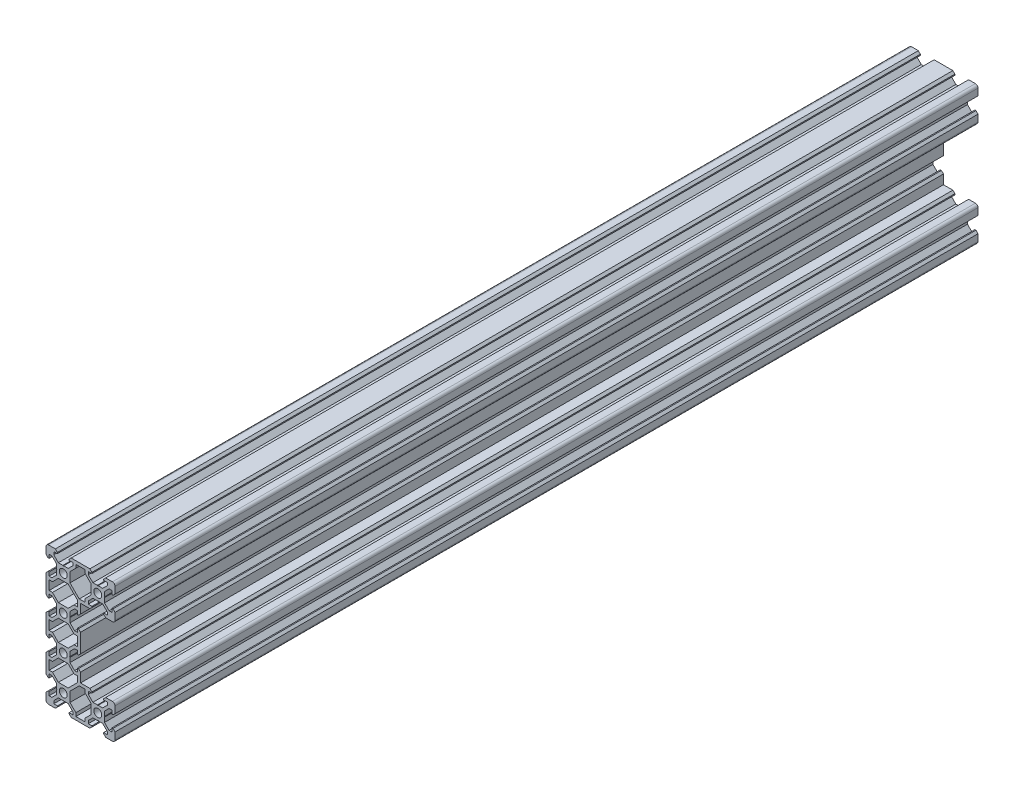
SolidWorks part; units mm, degrees
material "6061-T6 (SS)"
ref_plane "Front Plane" through (0, 0, 0) normal (0, 0, 1) x (1, 0, 0)
ref_plane "Top Plane" through (0, 0, 0) normal (0, 1, 0) x (1, 0, 0)
ref_plane "Right Plane" through (0, 0, 0) normal (1, 0, 0) x (0, 0, -1)
sketch "Sketch1" plane through (0, 0, 0) normal (0, 0, 1) x (1, 0, 0)
  line L0 (-20, -38.5) -> (-20, 38.5)
  line L1 (-18.5, 40) -> (18.5, 40)
  line L2 (20, 38.5) -> (20, 21.5)
  line L3 (18.5, 20) -> (0, 20)
  line L4 (0, 20) -> (0, -20)
  line L5 (0, 0) -> (-20, 0) construction
  line L6 (18.5, -20) -> (0, -20)
  line L7 (20, -38.5) -> (20, -21.5)
  line L8 (-18.5, -40) -> (18.5, -40)
  line L9 (20, 30) -> (10, 30) construction
  line L10 (-10, 0) -> (-10, 10) construction
  arc A0 (-18.5, -40) -> (-20, -38.5) centre (-18.5, -38.5) cw
  arc A1 (20, -38.5) -> (18.5, -40) centre (18.5, -38.5) cw
  arc A2 (18.5, -20) -> (20, -21.5) centre (18.5, -21.5) cw
  arc A3 (20, 21.5) -> (18.5, 20) centre (18.5, 21.5) cw
  arc A4 (18.5, 40) -> (20, 38.5) centre (18.5, 38.5) cw
  arc A5 (-20, 38.5) -> (-18.5, 40) centre (-18.5, 38.5) cw
  circle A6 centre (10, 30) radius 2.3
  circle A7 centre (-10, 30) radius 2.3
  circle A8 centre (-10, 10) radius 2.3
  circle A9 centre (-10, -10) radius 2.3
  circle A10 centre (10, -30) radius 2.3
  circle A11 centre (-10, -30) radius 2.3
  point P13 (-20, -40)
  point P16 (20, -40)
  point P19 (20, -20)
  point P22 (20, 20)
  point P25 (20, 40)
  point P28 (-20, 40)
  line B0 (-10, 30) -> (-10, 40) construction
  line B1 (-10, 33.69) -> (-10.21, 33.9)
  line B2 (-10.21, 33.9) -> (-12.8393, 33.9)
  line B3 (-12.8393, 33.9) -> (-15.5, 36.5607)
  line B4 (-15.5, 36.5607) -> (-15.5, 38.2)
  line B5 (-15.5, 38.2) -> (-13.395, 38.2)
  line B6 (-13.395, 38.2) -> (-13.395, 38.815)
  line B7 (-13.395, 38.815) -> (-14.58, 40)
  line B8 (-14.58, 40) -> (-5.42, 40)
  line B9 (-10, 30) -> (-15.9132, 35.9132) construction
  line B10 (-6.605, 38.815) -> (-5.42, 40)
  line B11 (-6.605, 38.2) -> (-6.605, 38.815)
  line B12 (-4.5, 38.2) -> (-6.605, 38.2)
  line B13 (-4.5, 36.5607) -> (-4.5, 38.2)
  line B14 (-7.1607, 33.9) -> (-4.5, 36.5607)
  line B15 (-9.79, 33.9) -> (-7.1607, 33.9)
  line B16 (-10, 33.69) -> (-9.79, 33.9)
  line B17 (10, 30) -> (10, 40) construction
  line B18 (10, 33.69) -> (9.79, 33.9)
  line B19 (9.79, 33.9) -> (7.1607, 33.9)
  line B20 (7.1607, 33.9) -> (4.5, 36.5607)
  line B21 (4.5, 36.5607) -> (4.5, 38.2)
  line B22 (4.5, 38.2) -> (6.605, 38.2)
  line B23 (6.605, 38.2) -> (6.605, 38.815)
  line B24 (6.605, 38.815) -> (5.42, 40)
  line B25 (5.42, 40) -> (14.58, 40)
  line B26 (10, 30) -> (4.0868, 35.9132) construction
  line B27 (13.395, 38.815) -> (14.58, 40)
  line B28 (13.395, 38.2) -> (13.395, 38.815)
  line B29 (15.5, 38.2) -> (13.395, 38.2)
  line B30 (15.5, 36.5607) -> (15.5, 38.2)
  line B31 (12.8393, 33.9) -> (15.5, 36.5607)
  line B32 (10.21, 33.9) -> (12.8393, 33.9)
  line B33 (10, 33.69) -> (10.21, 33.9)
  line B34 (10, -30) -> (10, -20) construction
  line B35 (10, -26.31) -> (9.79, -26.1)
  line B36 (9.79, -26.1) -> (7.1607, -26.1)
  line B37 (7.1607, -26.1) -> (4.5, -23.4393)
  line B38 (4.5, -23.4393) -> (4.5, -21.8)
  line B39 (4.5, -21.8) -> (6.605, -21.8)
  line B40 (6.605, -21.8) -> (6.605, -21.185)
  line B41 (6.605, -21.185) -> (5.42, -20)
  line B42 (5.42, -20) -> (14.58, -20)
  line B43 (10, -30) -> (4.0868, -24.0868) construction
  line B44 (13.395, -21.185) -> (14.58, -20)
  line B45 (13.395, -21.8) -> (13.395, -21.185)
  line B46 (15.5, -21.8) -> (13.395, -21.8)
  line B47 (15.5, -23.4393) -> (15.5, -21.8)
  line B48 (12.8393, -26.1) -> (15.5, -23.4393)
  line B49 (10.21, -26.1) -> (12.8393, -26.1)
  line B50 (10, -26.31) -> (10.21, -26.1)
  line B51 (-10, 30) -> (-20, 30) construction
  line B52 (-13.69, 30) -> (-13.9, 29.79)
  line B53 (-13.9, 29.79) -> (-13.9, 27.1607)
  line B54 (-13.9, 27.1607) -> (-16.5607, 24.5)
  line B55 (-16.5607, 24.5) -> (-18.2, 24.5)
  line B56 (-18.2, 24.5) -> (-18.2, 26.605)
  line B57 (-18.2, 26.605) -> (-18.815, 26.605)
  line B58 (-18.815, 26.605) -> (-20, 25.42)
  line B59 (-20, 25.42) -> (-20, 34.58)
  line B60 (-10, 30) -> (-15.9132, 24.0868) construction
  line B61 (-18.815, 33.395) -> (-20, 34.58)
  line B62 (-18.2, 33.395) -> (-18.815, 33.395)
  line B63 (-18.2, 35.5) -> (-18.2, 33.395)
  line B64 (-16.5607, 35.5) -> (-18.2, 35.5)
  line B65 (-13.9, 32.8393) -> (-16.5607, 35.5)
  line B66 (-13.9, 30.21) -> (-13.9, 32.8393)
  line B67 (-13.69, 30) -> (-13.9, 30.21)
  line B68 (-10, 10) -> (-20, 10) construction
  line B69 (-13.69, 10) -> (-13.9, 9.79)
  line B70 (-13.9, 9.79) -> (-13.9, 7.1607)
  line B71 (-13.9, 7.1607) -> (-16.5607, 4.5)
  line B72 (-16.5607, 4.5) -> (-18.2, 4.5)
  line B73 (-18.2, 4.5) -> (-18.2, 6.605)
  line B74 (-18.2, 6.605) -> (-18.815, 6.605)
  line B75 (-18.815, 6.605) -> (-20, 5.42)
  line B76 (-20, 5.42) -> (-20, 14.58)
  line B77 (-10, 10) -> (-15.9132, 4.0868) construction
  line B78 (-18.815, 13.395) -> (-20, 14.58)
  line B79 (-18.2, 13.395) -> (-18.815, 13.395)
  line B80 (-18.2, 15.5) -> (-18.2, 13.395)
  line B81 (-16.5607, 15.5) -> (-18.2, 15.5)
  line B82 (-13.9, 12.8393) -> (-16.5607, 15.5)
  line B83 (-13.9, 10.21) -> (-13.9, 12.8393)
  line B84 (-13.69, 10) -> (-13.9, 10.21)
  line B85 (-10, -10) -> (-20, -10) construction
  line B86 (-13.69, -10) -> (-13.9, -10.21)
  line B87 (-13.9, -10.21) -> (-13.9, -12.8393)
  line B88 (-13.9, -12.8393) -> (-16.5607, -15.5)
  line B89 (-16.5607, -15.5) -> (-18.2, -15.5)
  line B90 (-18.2, -15.5) -> (-18.2, -13.395)
  line B91 (-18.2, -13.395) -> (-18.815, -13.395)
  line B92 (-18.815, -13.395) -> (-20, -14.58)
  line B93 (-20, -14.58) -> (-20, -5.42)
  line B94 (-10, -10) -> (-15.9132, -15.9132) construction
  line B95 (-18.815, -6.605) -> (-20, -5.42)
  line B96 (-18.2, -6.605) -> (-18.815, -6.605)
  line B97 (-18.2, -4.5) -> (-18.2, -6.605)
  line B98 (-16.5607, -4.5) -> (-18.2, -4.5)
  line B99 (-13.9, -7.1607) -> (-16.5607, -4.5)
  line B100 (-13.9, -9.79) -> (-13.9, -7.1607)
  line B101 (-13.69, -10) -> (-13.9, -9.79)
  line B102 (-10, -30) -> (-20, -30) construction
  line B103 (-13.69, -30) -> (-13.9, -30.21)
  line B104 (-13.9, -30.21) -> (-13.9, -32.8393)
  line B105 (-13.9, -32.8393) -> (-16.5607, -35.5)
  line B106 (-16.5607, -35.5) -> (-18.2, -35.5)
  line B107 (-18.2, -35.5) -> (-18.2, -33.395)
  line B108 (-18.2, -33.395) -> (-18.815, -33.395)
  line B109 (-18.815, -33.395) -> (-20, -34.58)
  line B110 (-20, -34.58) -> (-20, -25.42)
  line B111 (-10, -30) -> (-15.9132, -35.9132) construction
  line B112 (-18.815, -26.605) -> (-20, -25.42)
  line B113 (-18.2, -26.605) -> (-18.815, -26.605)
  line B114 (-18.2, -24.5) -> (-18.2, -26.605)
  line B115 (-16.5607, -24.5) -> (-18.2, -24.5)
  line B116 (-13.9, -27.1607) -> (-16.5607, -24.5)
  line B117 (-13.9, -29.79) -> (-13.9, -27.1607)
  line B118 (-13.69, -30) -> (-13.9, -29.79)
  line B119 (-10, -30) -> (-10, -40) construction
  line B120 (-10, -33.69) -> (-9.79, -33.9)
  line B121 (-9.79, -33.9) -> (-7.1607, -33.9)
  line B122 (-7.1607, -33.9) -> (-4.5, -36.5607)
  line B123 (-4.5, -36.5607) -> (-4.5, -38.2)
  line B124 (-4.5, -38.2) -> (-6.605, -38.2)
  line B125 (-6.605, -38.2) -> (-6.605, -38.815)
  line B126 (-6.605, -38.815) -> (-5.42, -40)
  line B127 (-5.42, -40) -> (-14.58, -40)
  line B128 (-10, -30) -> (-4.0868, -35.9132) construction
  line B129 (-13.395, -38.815) -> (-14.58, -40)
  line B130 (-13.395, -38.2) -> (-13.395, -38.815)
  line B131 (-15.5, -38.2) -> (-13.395, -38.2)
  line B132 (-15.5, -36.5607) -> (-15.5, -38.2)
  line B133 (-12.8393, -33.9) -> (-15.5, -36.5607)
  line B134 (-10.21, -33.9) -> (-12.8393, -33.9)
  line B135 (-10, -33.69) -> (-10.21, -33.9)
  line B136 (10, -30) -> (10, -40) construction
  line B137 (10, -33.69) -> (10.21, -33.9)
  line B138 (10.21, -33.9) -> (12.8393, -33.9)
  line B139 (12.8393, -33.9) -> (15.5, -36.5607)
  line B140 (15.5, -36.5607) -> (15.5, -38.2)
  line B141 (15.5, -38.2) -> (13.395, -38.2)
  line B142 (13.395, -38.2) -> (13.395, -38.815)
  line B143 (13.395, -38.815) -> (14.58, -40)
  line B144 (14.58, -40) -> (5.42, -40)
  line B145 (10, -30) -> (15.9132, -35.9132) construction
  line B146 (6.605, -38.815) -> (5.42, -40)
  line B147 (6.605, -38.2) -> (6.605, -38.815)
  line B148 (4.5, -38.2) -> (6.605, -38.2)
  line B149 (4.5, -36.5607) -> (4.5, -38.2)
  line B150 (7.1607, -33.9) -> (4.5, -36.5607)
  line B151 (9.79, -33.9) -> (7.1607, -33.9)
  line B152 (10, -33.69) -> (9.79, -33.9)
  line B153 (10, 30) -> (10, 20) construction
  line B154 (10, 26.31) -> (10.21, 26.1)
  line B155 (10.21, 26.1) -> (12.8393, 26.1)
  line B156 (12.8393, 26.1) -> (15.5, 23.4393)
  line B157 (15.5, 23.4393) -> (15.5, 21.8)
  line B158 (15.5, 21.8) -> (13.395, 21.8)
  line B159 (13.395, 21.8) -> (13.395, 21.185)
  line B160 (13.395, 21.185) -> (14.58, 20)
  line B161 (14.58, 20) -> (5.42, 20)
  line B162 (10, 30) -> (15.9132, 24.0868) construction
  line B163 (6.605, 21.185) -> (5.42, 20)
  line B164 (6.605, 21.8) -> (6.605, 21.185)
  line B165 (4.5, 21.8) -> (6.605, 21.8)
  line B166 (4.5, 23.4393) -> (4.5, 21.8)
  line B167 (7.1607, 26.1) -> (4.5, 23.4393)
  line B168 (9.79, 26.1) -> (7.1607, 26.1)
  line B169 (10, 26.31) -> (9.79, 26.1)
  line B170 (-10, 10) -> (0, 10) construction
  line B171 (-6.31, 10) -> (-6.1, 10.21)
  line B172 (-6.1, 10.21) -> (-6.1, 12.8393)
  line B173 (-6.1, 12.8393) -> (-3.4393, 15.5)
  line B174 (-3.4393, 15.5) -> (-1.8, 15.5)
  line B175 (-1.8, 15.5) -> (-1.8, 13.395)
  line B176 (-1.8, 13.395) -> (-1.185, 13.395)
  line B177 (-1.185, 13.395) -> (0, 14.58)
  line B178 (0, 14.58) -> (0, 5.42)
  line B179 (-10, 10) -> (-4.0868, 15.9132) construction
  line B180 (-1.185, 6.605) -> (0, 5.42)
  line B181 (-1.8, 6.605) -> (-1.185, 6.605)
  line B182 (-1.8, 4.5) -> (-1.8, 6.605)
  line B183 (-3.4393, 4.5) -> (-1.8, 4.5)
  line B184 (-6.1, 7.1607) -> (-3.4393, 4.5)
  line B185 (-6.1, 9.79) -> (-6.1, 7.1607)
  line B186 (-6.31, 10) -> (-6.1, 9.79)
  line B187 (-10, -10) -> (0, -10) construction
  line B188 (-6.31, -10) -> (-6.1, -9.79)
  line B189 (-6.1, -9.79) -> (-6.1, -7.1607)
  line B190 (-6.1, -7.1607) -> (-3.4393, -4.5)
  line B191 (-3.4393, -4.5) -> (-1.8, -4.5)
  line B192 (-1.8, -4.5) -> (-1.8, -6.605)
  line B193 (-1.8, -6.605) -> (-1.185, -6.605)
  line B194 (-1.185, -6.605) -> (0, -5.42)
  line B195 (0, -5.42) -> (0, -14.58)
  line B196 (-10, -10) -> (-4.0868, -4.0868) construction
  line B197 (-1.185, -13.395) -> (0, -14.58)
  line B198 (-1.8, -13.395) -> (-1.185, -13.395)
  line B199 (-1.8, -15.5) -> (-1.8, -13.395)
  line B200 (-3.4393, -15.5) -> (-1.8, -15.5)
  line B201 (-6.1, -12.8393) -> (-3.4393, -15.5)
  line B202 (-6.1, -10.21) -> (-6.1, -12.8393)
  line B203 (-6.31, -10) -> (-6.1, -10.21)
  line B204 (10, -30) -> (20, -30) construction
  line B205 (13.69, -30) -> (13.9, -29.79)
  line B206 (13.9, -29.79) -> (13.9, -27.1607)
  line B207 (13.9, -27.1607) -> (16.5607, -24.5)
  line B208 (16.5607, -24.5) -> (18.2, -24.5)
  line B209 (18.2, -24.5) -> (18.2, -26.605)
  line B210 (18.2, -26.605) -> (18.815, -26.605)
  line B211 (18.815, -26.605) -> (20, -25.42)
  line B212 (20, -25.42) -> (20, -34.58)
  line B213 (10, -30) -> (15.9132, -24.0868) construction
  line B214 (18.815, -33.395) -> (20, -34.58)
  line B215 (18.2, -33.395) -> (18.815, -33.395)
  line B216 (18.2, -35.5) -> (18.2, -33.395)
  line B217 (16.5607, -35.5) -> (18.2, -35.5)
  line B218 (13.9, -32.8393) -> (16.5607, -35.5)
  line B219 (13.9, -30.21) -> (13.9, -32.8393)
  line B220 (13.69, -30) -> (13.9, -30.21)
  line B221 (10, 30) -> (20, 30) construction
  line B222 (13.69, 30) -> (13.9, 30.21)
  line B223 (13.9, 30.21) -> (13.9, 32.8393)
  line B224 (13.9, 32.8393) -> (16.5607, 35.5)
  line B225 (16.5607, 35.5) -> (18.2, 35.5)
  line B226 (18.2, 35.5) -> (18.2, 33.395)
  line B227 (18.2, 33.395) -> (18.815, 33.395)
  line B228 (18.815, 33.395) -> (20, 34.58)
  line B229 (20, 34.58) -> (20, 25.42)
  line B230 (10, 30) -> (15.9132, 35.9132) construction
  line B231 (18.815, 26.605) -> (20, 25.42)
  line B232 (18.2, 26.605) -> (18.815, 26.605)
  line B233 (18.2, 24.5) -> (18.2, 26.605)
  line B234 (16.5607, 24.5) -> (18.2, 24.5)
  line B235 (13.9, 27.1607) -> (16.5607, 24.5)
  line B236 (13.9, 29.79) -> (13.9, 27.1607)
  line B237 (13.69, 30) -> (13.9, 29.79)
  line B238 (-18.2, -2.7) -> (-18.2, 2.7)
  line B239 (-18.2, 2.7) -> (-16.2393, 2.7)
  line B240 (-16.2393, 2.7) -> (-12.8393, 6.1)
  line B241 (-12.8393, 6.1) -> (-7.1607, 6.1)
  line B242 (-10, 6.1) -> (-10, 0) construction
  line B243 (-10, 0) -> (-18.2, 0) construction
  line B244 (-3.7607, 2.7) -> (-7.1607, 6.1)
  line B245 (-1.8, 2.7) -> (-3.7607, 2.7)
  line B246 (-1.8, -2.7) -> (-1.8, 2.7)
  line B247 (-1.8, -2.7) -> (-3.7607, -2.7)
  line B248 (-3.7607, -2.7) -> (-7.1607, -6.1)
  line B249 (-12.8393, -6.1) -> (-7.1607, -6.1)
  line B250 (-16.2393, -2.7) -> (-12.8393, -6.1)
  line B251 (-18.2, -2.7) -> (-16.2393, -2.7)
  line B252 (-10, 6.1) -> (-10, 10) construction
  line B253 (-10, 10) -> (-15.0927, 4.9073) construction
  line B254 (-18.2, 17.3) -> (-18.2, 22.7)
  line B255 (-18.2, 22.7) -> (-16.2393, 22.7)
  line B256 (-16.2393, 22.7) -> (-12.8393, 26.1)
  line B257 (-12.8393, 26.1) -> (-7.1607, 26.1)
  line B258 (-10, 26.1) -> (-10, 20) construction
  line B259 (-10, 20) -> (-18.2, 20) construction
  line B260 (-1.8, 17.3) -> (-3.7607, 17.3)
  line B261 (-3.7607, 17.3) -> (-7.1607, 13.9)
  line B262 (-12.8393, 13.9) -> (-7.1607, 13.9)
  line B263 (-16.2393, 17.3) -> (-12.8393, 13.9)
  line B264 (-18.2, 17.3) -> (-16.2393, 17.3)
  line B265 (-10, 26.1) -> (-10, 30) construction
  line B266 (-10, 30) -> (-15.0927, 24.9073) construction
  line B267 (-7.1607, 26.1) -> (-1.8, 20.7393)
  line B268 (-1.8, 17.3) -> (-1.8, 20.7393)
  line B269 (2.7, -38.2) -> (-2.7, -38.2)
  line B270 (-2.7, -38.2) -> (-2.7, -36.2393)
  line B271 (-2.7, -36.2393) -> (-6.1, -32.8393)
  line B272 (-6.1, -32.8393) -> (-6.1, -27.1607)
  line B273 (-6.1, -30) -> (0, -30) construction
  line B274 (0, -30) -> (0, -38.2) construction
  line B275 (2.7, -21.8) -> (2.7, -23.7607)
  line B276 (2.7, -23.7607) -> (6.1, -27.1607)
  line B277 (6.1, -32.8393) -> (6.1, -27.1607)
  line B278 (2.7, -36.2393) -> (6.1, -32.8393)
  line B279 (2.7, -38.2) -> (2.7, -36.2393)
  line B280 (-6.1, -30) -> (-10, -30) construction
  line B281 (-10, -30) -> (-4.9073, -35.0927) construction
  line B282 (-6.1, -27.1607) -> (-0.7393, -21.8)
  line B283 (2.7, -21.8) -> (-0.7393, -21.8)
  line B284 (-18.2, -22.7) -> (-18.2, -17.3)
  line B285 (-18.2, -17.3) -> (-16.2393, -17.3)
  line B286 (-16.2393, -17.3) -> (-12.8393, -13.9)
  line B287 (-12.8393, -13.9) -> (-7.1607, -13.9)
  line B288 (-10, -13.9) -> (-10, -20) construction
  line B289 (-10, -20) -> (-18.2, -20) construction
  line B290 (-12.8393, -26.1) -> (-7.1607, -26.1)
  line B291 (-16.2393, -22.7) -> (-12.8393, -26.1)
  line B292 (-18.2, -22.7) -> (-16.2393, -22.7)
  line B293 (-10, -13.9) -> (-10, -10) construction
  line B294 (-10, -10) -> (-15.0927, -15.0927) construction
  line B295 (-3.7607, -17.3) -> (-7.1607, -13.9)
  line B296 (-1.8, -17.3) -> (-3.7607, -17.3)
  line B297 (-1.8, -17.3) -> (-1.8, -20.7393)
  line B298 (-1.8, -20.7393) -> (-7.1607, -26.1)
  line B299 (-2.7, 38.2) -> (2.7, 38.2)
  line B300 (2.7, 38.2) -> (2.7, 36.2393)
  line B301 (2.7, 36.2393) -> (6.1, 32.8393)
  line B302 (6.1, 32.8393) -> (6.1, 27.1607)
  line B303 (6.1, 30) -> (0, 30) construction
  line B304 (0, 30) -> (0, 38.2) construction
  line B305 (-6.1, 32.8393) -> (-6.1, 27.1607)
  line B306 (-2.7, 36.2393) -> (-6.1, 32.8393)
  line B307 (-2.7, 38.2) -> (-2.7, 36.2393)
  line B308 (6.1, 30) -> (10, 30) construction
  line B309 (10, 30) -> (4.9073, 35.0927) construction
  line B310 (2.7, 23.7607) -> (6.1, 27.1607)
  line B311 (2.7, 21.8) -> (2.7, 23.7607)
  line B312 (2.7, 21.8) -> (-0.7393, 21.8)
  line B313 (-0.7393, 21.8) -> (-6.1, 27.1607)
sketch_block_instance "V Slot 2-1"
sketch_block "V Slot 2" parameters "D1"=10, "D2"=11, "D3"=4.3, "D4"=1.8, "D5"=0.21, "D6"=45, "D7"=9.16, "D8"=1.5, "D9"=6.79
sketch_block_instance "V Slot 2-2"
sketch_block_instance "V Slot 2-3"
sketch_block_instance "V Slot 2-4"
sketch_block_instance "V Slot 2-5"
sketch_block_instance "V Slot 2-6"
sketch_block_instance "V Slot 2-7"
sketch_block_instance "V Slot 2-8"
sketch_block_instance "V Slot 2-9"
sketch_block_instance "V Slot 2-10"
sketch_block_instance "V Slot 2-11"
sketch_block_instance "V Slot 2-12"
sketch_block_instance "V Slot 2-13"
sketch_block_instance "V Slot 2-14"
sketch_block_instance "Center Cutout 1-1"
sketch_block "Center Cutout 1" parameters "D1"=5.4, "D2"=12.2, "D3"=8.2, "D4"=45, "D5"=10, "D6"=1.5
sketch_block_instance "Corner Cutout 1-1"
sketch_block "Corner Cutout 1" parameters "D1"=5.4, "D2"=12.2, "D3"=8.2, "D4"=45, "D5"=10, "D6"=1.5
sketch_block_instance "Corner Cutout 1-2"
sketch_block_instance "Corner Cutout 2-1"
sketch_block "Corner Cutout 2" parameters "D1"=5.4, "D2"=12.2, "D3"=8.2, "D4"=45, "D5"=10, "D6"=1.5
sketch_block_instance "Corner Cutout 2-2" parameters "D3"=1.5, "D6"=5.6161, "D7"=4.6, "D8"=4.6, "D1"=58.7796, "D2"=101.8341, "D4"=37, "D5"=40
extrude "Boss-Extrude1" add sketch "Sketch1" along normal blind 500 contours B237 B222 B223 B224 B225 B226 B227 B228 L2 A4 L1 B27 B28 B29 B30 B31 B32 B33 B18 B19 B20 B21 B22 B23 B24 B10 B11 B12 B13 B14 B15 B16 B1 B2 B3 B4 B5 B6 B7 A5 L0 B61 B62 B63 B64 B65 B66 B67 B52
